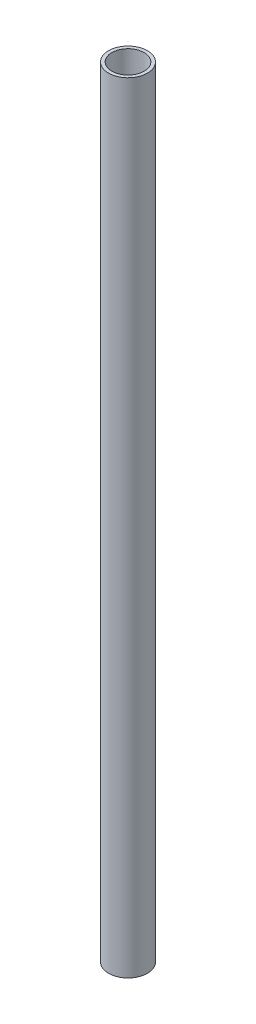
SolidWorks part; units mm, degrees
material "6061-T6 (SS)"
ref_plane "Front Plane" through (0, 0, 0) normal (0, 0, 1) x (1, 0, 0)
ref_plane "Top Plane" through (0, 0, 0) normal (0, 1, 0) x (1, 0, 0)
ref_plane "Right Plane" through (0, 0, 0) normal (1, 0, 0) x (0, 0, -1)
sketch "Sketch1" plane through (0, 0, 0) normal (0, 1, 0) x (1, 0, 0)
  circle A0 centre (0, 0) radius 21.082
  circle A1 centre (0, 0) radius 17.526
  dimension "D1" = 42.164
  dimension "D2" = 35.052
extrude "Boss-Extrude1" add sketch "Sketch1" along normal blind 844.55
